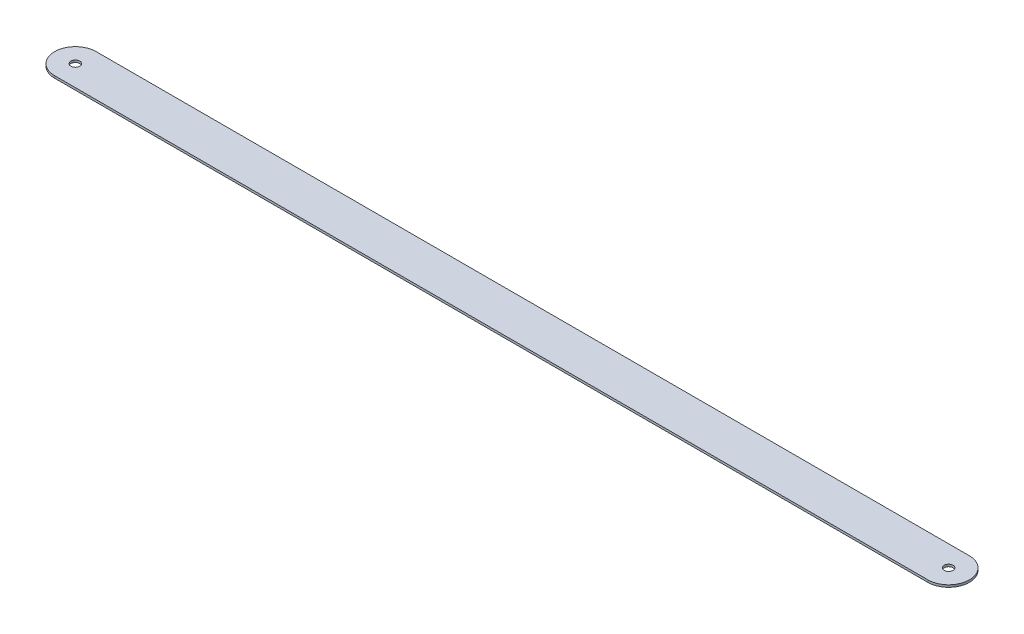
SolidWorks part; units mm, degrees
ref_plane "Front Plane" through (0, 0, 0) normal (0, 0, 1) x (1, 0, 0)
ref_plane "Top Plane" through (0, 0, 0) normal (0, 1, 0) x (1, 0, 0)
ref_plane "Right Plane" through (0, 0, 0) normal (1, 0, 0) x (0, 0, -1)
sketch "Sketch1" plane through (0, 0, 0) normal (0, 1, 0) x (1, 0, 0)
  line L0 (0, 0) -> (587.63, 0) construction
  line L1 (0, 14) -> (587.63, 14)
  line L2 (0, -14) -> (587.63, -14)
  arc A0 (0, 14) -> (0, -14) centre (0, 0) ccw
  arc A1 (587.63, -14) -> (587.63, 14) centre (587.63, 0) ccw
  circle A2 centre (0, 0) radius 3
  circle A3 centre (587.63, 0) radius 3
  point P3 (293.815, 0)
  dimension "D1" = 6
  dimension "D2" = 14
  dimension "D3" = 587.63
extrude "Boss-Extrude1" add sketch "Sketch1" along normal blind 1.5
